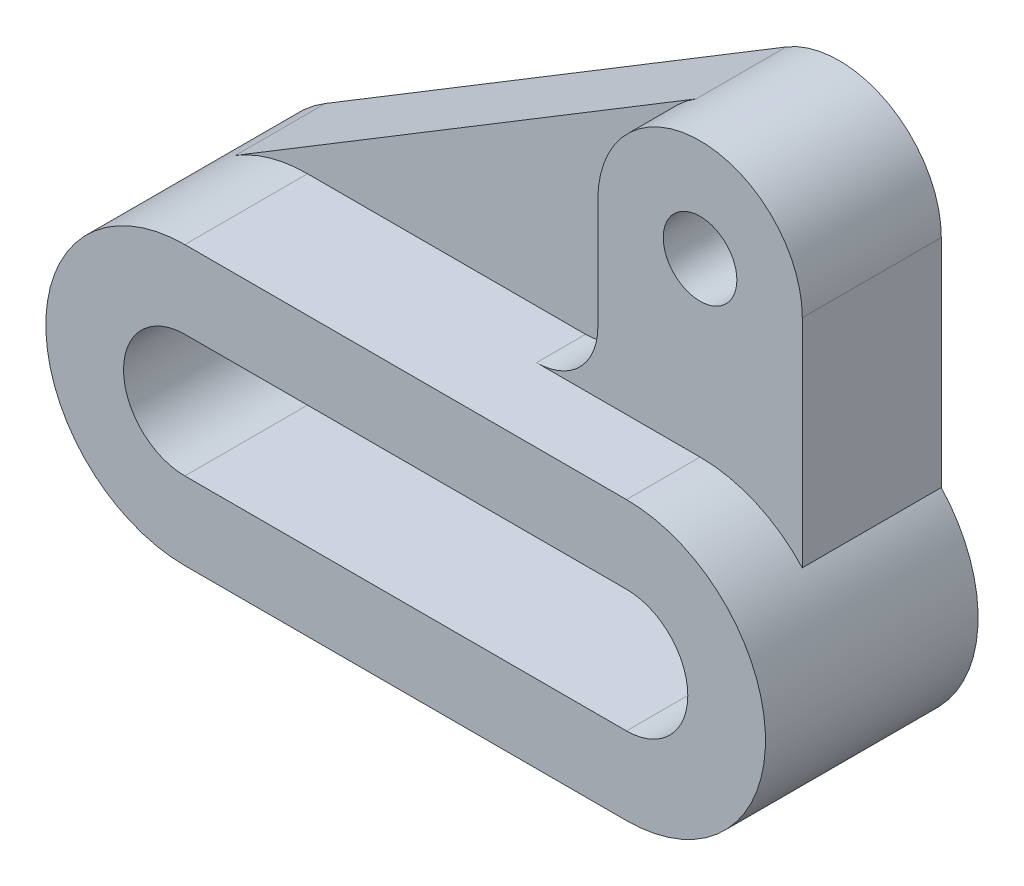
SolidWorks part; units mm, degrees
ref_plane "Ön Düzlem" through (0, 0, 0) normal (0, 0, 1) x (1, 0, 0)
ref_plane "Üst Düzlem" through (0, 0, 0) normal (0, 1, 0) x (1, 0, 0)
ref_plane "Sağ Düzlem" through (0, 0, 0) normal (1, 0, 0) x (0, 0, -1)
sketch "Çizim1" plane through (0, 0, 0) normal (0, 0, 1) x (1, 0, 0)
  line L0 (-54, 0) -> (54, 0) construction
  line L1 (-54, 15) -> (54, 15)
  line L2 (-54, -15) -> (54, -15)
  line L3 (-54, 0) -> (54, 0) construction
  line L4 (-54, 34) -> (54, 34)
  line L5 (-54, -34) -> (54, -34)
  arc A0 (-54, 15) -> (-54, -15) centre (-54, 0) ccw
  arc A1 (54, -15) -> (54, 15) centre (54, 0) ccw
  arc A2 (-54, 34) -> (-54, -34) centre (-54, 0) ccw
  arc A3 (54, -34) -> (54, 34) centre (54, 0) ccw
  point P2 (0, 0)
  point P10 (0, 0)
  dimension "D2" = 15
  dimension "D3" = 34
  dimension "D1" = 108
extrude "Yükseklik-Ekstrüzyon1" add sketch "Çizim1" against normal blind 52
ref_plane "Düzlem1" through (0, 0, -18) normal (0, 0, 1) x (1, 0, 0)
sketch "Çizim3" plane through (0, 0, -18) normal (0, 0, 1) x (1, 0, 0)
  line L0 (54, 0) -> (54, 76) construction
  line L1 (54, 76) -> (29, 76) construction
  line L2 (54, 76) -> (79, 76) construction
  line L3 (29, 76) -> (29, 49)
  line L4 (54, 34) -> (-54, 34) construction
  line L5 (-54, 0) -> (54, 0) construction
  line L6 (79, 76) -> (79, 23.0434)
  line L7 (-54, 34) -> (54, 34)
  line L8 (-54, 0) -> (54, 0) construction
  line L9 (-54, 15) -> (54, 15)
  line L10 (-54, -15) -> (54, -15)
  line L11 (-54, -34) -> (54, -34)
  circle A0 centre (54, 76) radius 9
  arc A1 (79, 76) -> (29, 76) centre (54, 76) ccw
  arc A2 (-54, 34) -> (-54, -34) centre (-54, 0) ccw
  arc A3 (14, 34) -> (29, 49) centre (14, 49) ccw
  arc A4 (54, -34) -> (54, 34) centre (54, 0) ccw construction
  arc A5 (-54, 15) -> (-54, -15) centre (-54, 0) ccw
  arc A6 (54, -15) -> (54, 15) centre (54, 0) ccw
  arc A7 (54, -34) -> (54, 34) centre (54, 0) ccw
  point P14 (0, 0)
  point P24 (0, 0)
  dimension "D2" = 18
  dimension "D3" = 50
  dimension "D4" = 15
  dimension "D6" = 15
  dimension "D5" = 34
  dimension "D1" = 76
extrude "Yükseklik-Ekstrüzyon2" add sketch "Çizim3" against normal blind 34 contours A7 L6 A1 L3 A3 L7 A0
ref_plane "Düzlem2" through (0, 0, -30) normal (0, 0, 1) x (1, 0, 0)
sketch "Çizim4" plane through (0, 0, -30) normal (0, 0, 1) x (1, 0, 0)
  line L0 (-71.6263, 29.0743) -> (41.0395, 97.3781)
  arc A2 (-54, 34) -> (-54, -34) centre (-54, 0) ccw construction
  arc A6 (79, 76) -> (29, 76) centre (54, 76) ccw construction
rib "Feder1" sketch "Çizim4" sketch "Çizim4" thickness 22 extrusion direction parallel to sketch draft on no parameters "D1"=22
